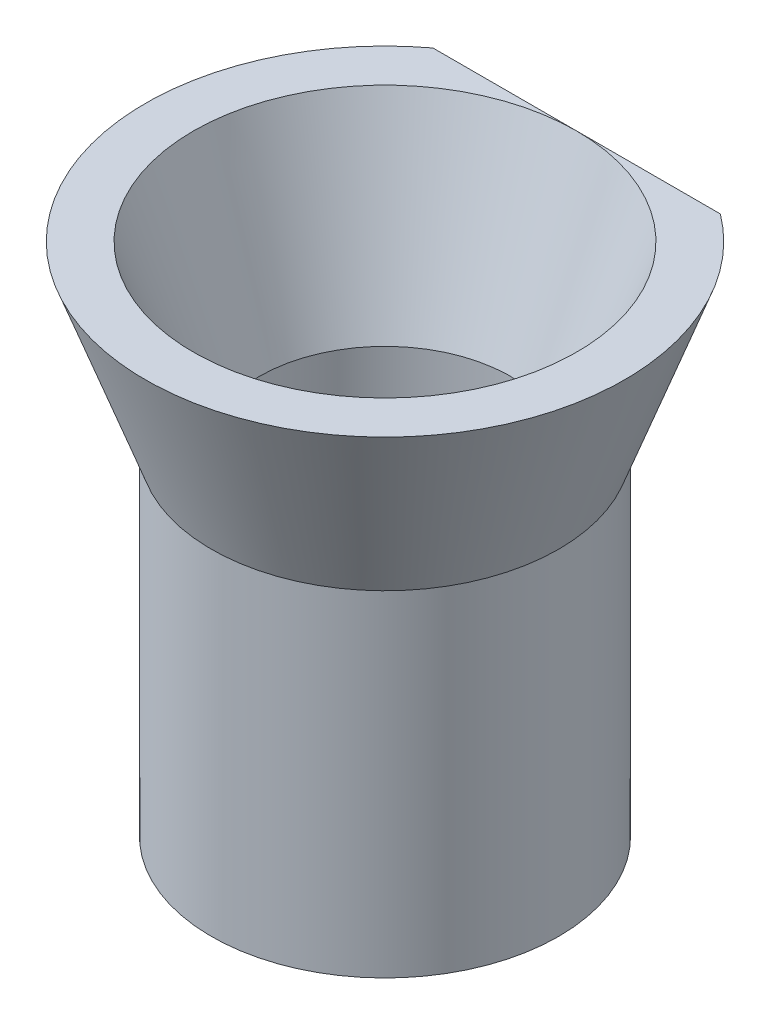
SolidWorks part; units mm, degrees
ref_plane "Alzado" through (0, 0, 0) normal (0, 0, 1) x (1, 0, 0)
ref_plane "Planta" through (0, 0, 0) normal (0, 1, 0) x (1, 0, 0)
ref_plane "Vista lateral" through (0, 0, 0) normal (1, 0, 0) x (0, 0, -1)
sketch "Croquis2" plane through (0, 0, 0) normal (0, 0, 1) x (1, 0, 0)
  line L0 (0, 0) -> (-5.25, 0) construction
  line L1 (-5.25, 0) -> (-8, 7.5)
  line L2 (-8, 7.5) -> (0, 7.5) construction
  line L3 (0, 7.5) -> (0, 0) construction
  line L4 (-8, 7.5) -> (-10, 7.5)
  line L5 (-10, 7.5) -> (-7.25, 0)
  line L6 (-7.25, 0) -> (-5.25, 0)
  dimension "D1" = 7.5
  dimension "D2" = 8
  dimension "D3" = 5.25
  dimension "D4" = 2
  dimension "D5" = 2
revolve "Revolución1" add sketch "Croquis2" angle 360 about L3
sketch "Croquis3" plane through (0, 0, 0) normal (0, -1, 0) x (1, 0, 0)
  circle A0 centre (0, 0) radius 5.25
  circle A1 centre (0, 0) radius 7.25
extrude "Saliente-Extruir1" add sketch "Croquis3" along normal blind 14
sketch "Croquis4" plane through (0, 7.5, 0) normal (0, 1, 0) x (1, 0, 0)
  line L0 (-7.4798, 8) -> (7.4798, 8)
  line L1 (7.4798, 8) -> (7.4798, 11.2455)
  line L2 (7.4798, 11.2455) -> (-7.4798, 11.2455)
  line L3 (-7.4798, 11.2455) -> (-7.4798, 8)
  point P3 (0, 8)
extrude "Cortar-Extruir1" cut sketch "Croquis4" against normal blind 10
